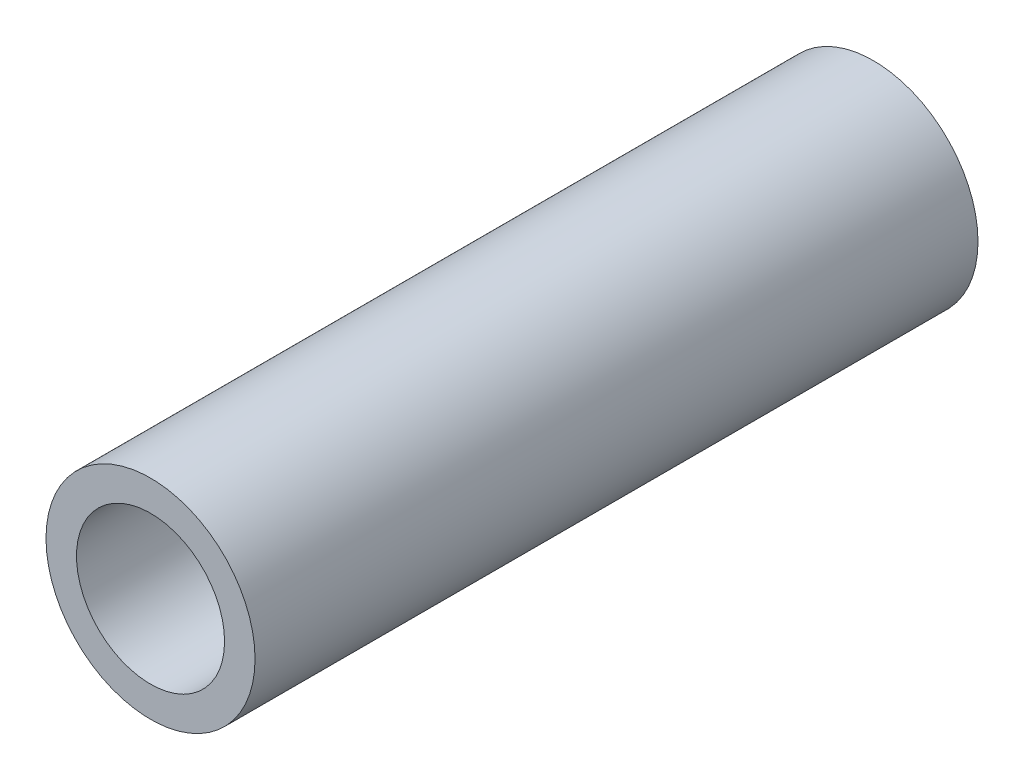
SolidWorks part; units mm, degrees
material "1.0545 (S355N)"
ref_plane "Front Plane" through (0, 0, 0) normal (0, 0, 1) x (1, 0, 0)
ref_plane "Top Plane" through (0, 0, 0) normal (0, 1, 0) x (1, 0, 0)
ref_plane "Right Plane" through (0, 0, 0) normal (1, 0, 0) x (0, 0, -1)
sketch "Sketch1" plane through (0, 0, 0) normal (0, 0, 1) x (1, 0, 0)
  circle A0 centre (0, 0) radius 8.5
  circle A1 centre (0, 0) radius 12
  dimension "di" = 17
  dimension "da" = 24
extrude "Boss-Extrude1" add sketch "Sketch1" along normal mid plane 83
